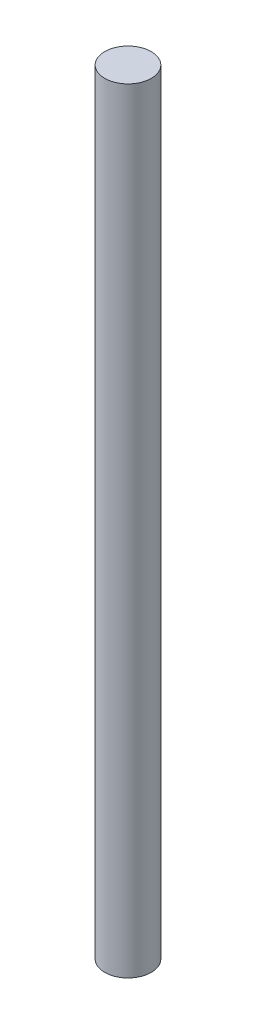
SolidWorks part; units mm, degrees
ref_plane "Alzado" through (0, 0, 0) normal (0, 0, 1) x (1, 0, 0)
ref_plane "Planta" through (0, 0, 0) normal (0, 1, 0) x (1, 0, 0)
ref_plane "Vista lateral" through (0, 0, 0) normal (1, 0, 0) x (0, 0, -1)
sketch "Croquis1" plane through (0, 0, 0) normal (0, 1, 0) x (1, 0, 0)
  circle A0 centre (0, 0) radius 3
  dimension "D1" = 6
extrude "Saliente-Extruir1" add sketch "Croquis1" along normal blind 100
